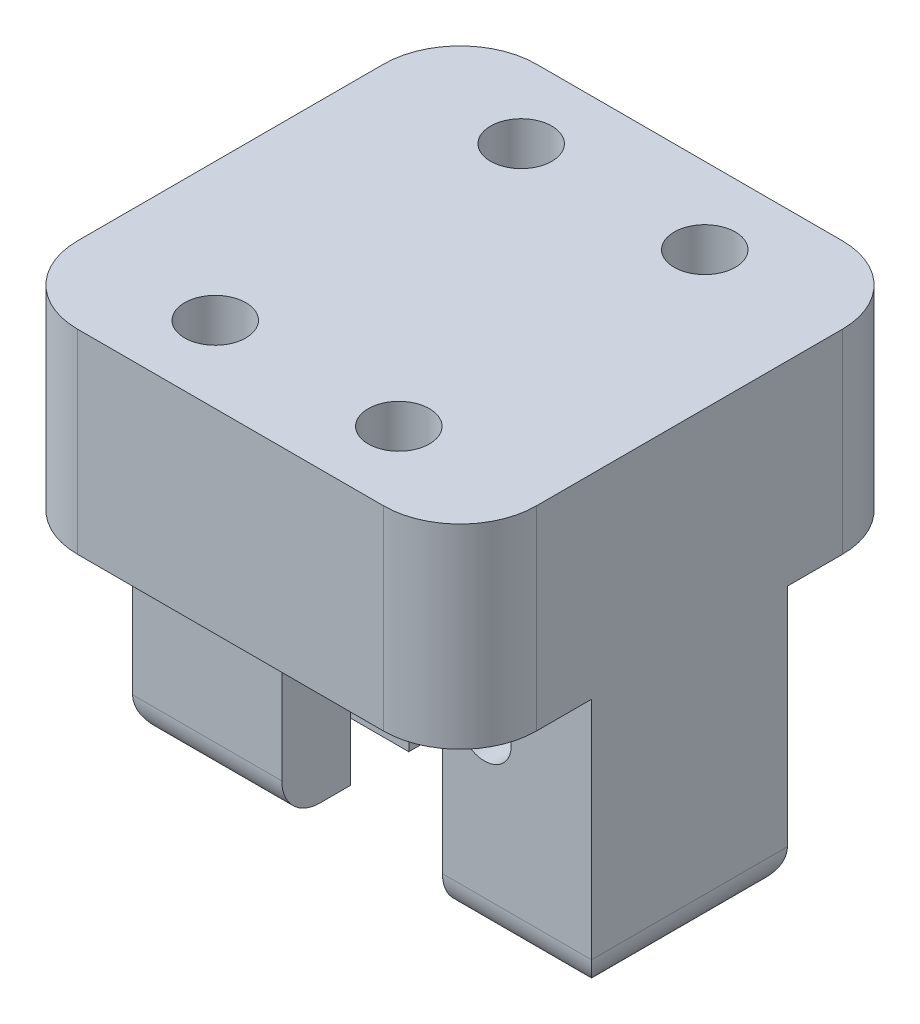
SolidWorks part; units mm, degrees
ref_plane "Front Plane" through (0, 0, 0) normal (0, 0, 1) x (1, 0, 0)
ref_plane "Top Plane" through (0, 0, 0) normal (0, 1, 0) x (1, 0, 0)
ref_plane "Right Plane" through (0, 0, 0) normal (1, 0, 0) x (0, 0, -1)
sketch "Sketch2" plane through (0, 0, 0) normal (0, 1, 0) x (1, 0, 0)
  line L1 (-15, -15) -> (15, -15)
  line L2 (-15, -15) -> (-15, 15)
  line L3 (-15, 15) -> (15, 15)
  line L4 (15, -15) -> (15, 15)
  line L5 (-15, -15) -> (15, 15) construction
  line L6 (-15, 15) -> (15, -15) construction
  point P0 (0, 0)
  dimension "D1" = 30
  dimension "D2" = 30
extrude "Boss-Extrude1" add sketch "Sketch2" along normal blind 30
sketch "Sketch3" plane through (0, 0, 15) normal (0, 0, 1) x (1, 0, 0)
  line L0 (0, 0) -> (0, 30) construction
  line L1 (-15, 30) -> (15, 30) construction
  line L2 (-5.25, 12) -> (-5.25, 0)
  line L3 (-15, 0) -> (15, 0) construction
  line L4 (-5.25, 0) -> (5.25, 0)
  line L5 (-5.25, 12) -> (5.25, 12)
  line L6 (5.25, 12) -> (5.25, 0)
  line L7 (0, 12) -> (-15, 12) construction
  line L8 (-15, 30) -> (-15, 0) construction
  circle A0 centre (0, 12) radius 5.25
  circle A1 centre (-8, 12) radius 1.75
  circle A2 centre (8, 12) radius 1.75
  line M7 (-15, 0) -> (15, 0)
  dimension "D1" = 18
  dimension "D2" = 10.5
  dimension "D3" = 3.5
  dimension "D4" = 8
extrude "Cut-Extrude1" cut sketch "Sketch3" against normal up to next contours A1 | A2 | L5 A0 | L5 A0 | A0 L2 L6 M7
sketch "Sketch4" plane through (0, 0, 15) normal (0, 0, 1) x (1, 0, 0)
  line L0 (-11.25, 12) -> (-11.25, 0)
  line L1 (-15, 0) -> (-5.25, 0) construction
  line L2 (11.25, 12) -> (11.25, 0)
  line L3 (5.25, 0) -> (15, 0) construction
  line L4 (11.25, 0) -> (-11.25, 0)
  line L5 (-11.25, 12) -> (11.25, 12)
  circle A0 centre (0, 12) radius 11.25
  circle M1 centre (-8, 12) radius 1.75
  line M7 (-15, 0) -> (-5.25, 0)
  line M8 (-5.25, 0) -> (-5.25, 12)
  dimension "D1" = 22.5
extrude "Cut-Extrude2" cut sketch "Sketch4" against normal blind 1.9 and the other way blind 1.9 from offset 15 contours A0 L0 M7 M8 | L5 A0 M8 M1 offset against normal yes
sketch "Sketch5" plane through (0, 30, 0) normal (0, 1, 0) x (1, 0, 0)
  line L0 (0, 15) -> (0, -15) construction
  line L1 (15, 15) -> (-15, 15) construction
  line L2 (-15, -15) -> (15, -15) construction
  line L3 (-15, 0) -> (15, 0) construction
  line L4 (-15, 15) -> (-15, -15) construction
  line L5 (15, -15) -> (15, 15) construction
  circle A0 centre (-6, 10) radius 2
  circle A1 centre (6, 10) radius 2
  circle A2 centre (6, -10) radius 2
  circle A3 centre (-6, -10) radius 2
  dimension "D1" = 6
  dimension "D2" = 4
  dimension "D3" = 5
extrude "Cut-Extrude3" cut sketch "Sketch5" against normal up to next
sketch "Sketch6" plane through (0, 0, 0) normal (0, -1, 0) x (1, 0, 0)
  line L0 (0, 15) -> (0, 0) construction
  line L1 (5.25, 15) -> (-5.25, 15) construction
  line L2 (0, 0) -> (-15, 0) construction
  line L3 (-15, -15) -> (-15, 15) construction
  line L4 (15, 15) -> (15, -15) construction
  line L5 (-15, 15) -> (15, 15)
  line L6 (-15, 15) -> (-15, 6.4)
  line L7 (-15, 6.4) -> (15, 6.4)
  line L8 (15, 15) -> (15, 6.4)
  line L9 (-11.25, 1.9) -> (-5.25, 1.9) construction
  line L10 (-15, -6.4) -> (15, -6.4)
  line L11 (15, -15) -> (15, -6.4)
  line L12 (-15, -15) -> (15, -15)
  line L13 (-15, -15) -> (-15, -6.4)
  dimension "D2" = 4.5
extrude "Cut-Extrude5" cut sketch "Sketch6" against normal blind 17.25
sketch "Sketch8" plane through (0, 17.25, 0) normal (0, -1, 0) x (1, 0, 0)
  line L1 (0, 15) -> (0, 0) construction
  line L2 (15, 15) -> (-15, 15) construction
  line L3 (0, 0) -> (-11.25, 0) construction
  line L4 (-11.25, 1.9) -> (-11.25, -1.9) construction
  circle A0 centre (-6, 10) radius 3.6
  circle A1 centre (6, 10) radius 3.6
  circle A2 centre (6, -10) radius 3.6
  circle A3 centre (-6, -10) radius 3.6
  dimension "D1" = 7.2
extrude "Cut-Extrude6" cut sketch "Sketch8" against normal blind 2
fillet "Fillet1" radius 5 4 edges at (15, 23.625, -15) (15, 23.625, 15) (-15, 23.625, 15) (-15, 23.625, -15)
fillet "Fillet2" radius 2.5 6 edges at (10.125, 0, -6.4) (15, 0, 0) (10.125, 0, 6.4) (-10.125, 0, -6.4) (-10.125, 0, 6.4) (-15, 0, 0)
